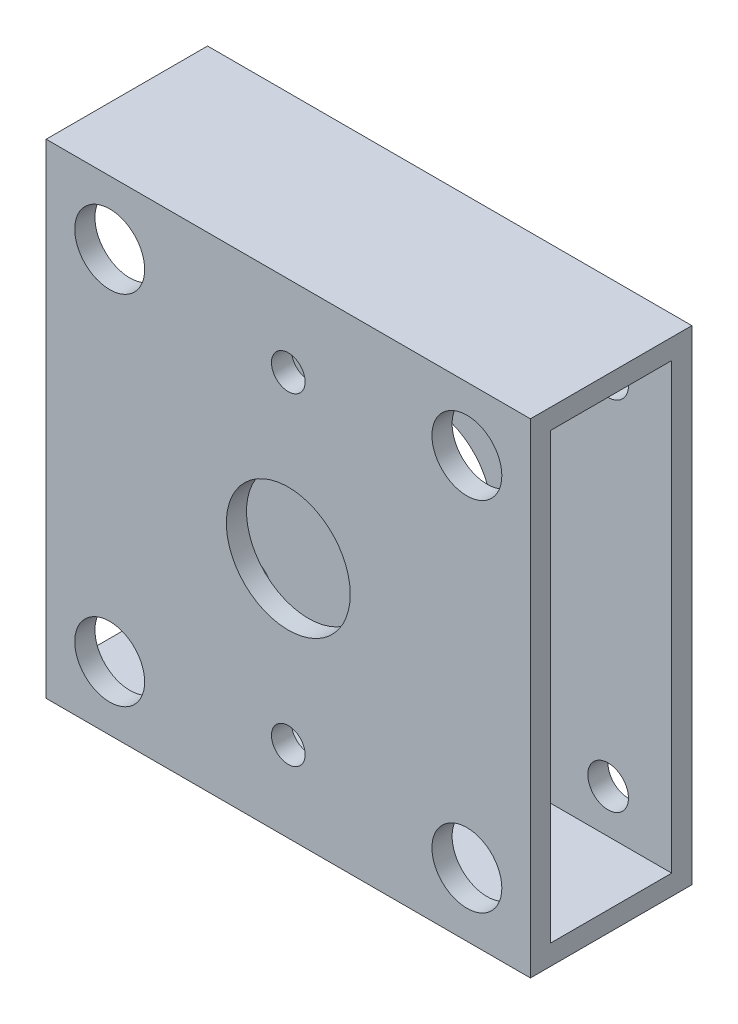
SolidWorks part; units mm, degrees
material "ALUMINUM 6061-T6"
ref_plane "Front Plane" through (0, 0, 0) normal (0, 0, 1) x (1, 0, 0)
ref_plane "Top Plane" through (0, 0, 0) normal (0, 1, 0) x (1, 0, 0)
ref_plane "Right Plane" through (0, 0, 0) normal (1, 0, 0) x (0, 0, -1)
sketch "Sketch1" plane through (0, 0, 0) normal (0, 0, 1) x (1, 0, 0)
  line L1 (-38.1, -38.1) -> (38.1, -38.1)
  line L2 (-38.1, -38.1) -> (-38.1, 38.1)
  line L3 (-38.1, 38.1) -> (38.1, 38.1)
  line L4 (38.1, -38.1) -> (38.1, 38.1)
  line L5 (-38.1, -38.1) -> (38.1, 38.1) construction
  line L6 (-38.1, 38.1) -> (38.1, -38.1) construction
  point P0 (0, 0)
  dimension "D1" = 76.2
  dimension "D2" = 76.2
extrude "Boss-Extrude1" add sketch "Sketch1" along normal mid plane 25.4
sketch "Sketch2" plane through (38.1, 0, 0) normal (1, 0, 0) x (0, 0, -1)
  line L8 (9.525, -34.925) -> (9.525, 34.925)
  line L9 (9.525, 34.925) -> (-9.525, 34.925)
  line L10 (-9.525, 34.925) -> (-9.525, -34.925)
  line L11 (-9.525, -34.925) -> (9.525, -34.925)
  line L12 (9.525, -34.925) -> (9.525, 34.925)
  line L13 (9.525, 34.925) -> (-9.525, 34.925)
  line L14 (-9.525, 34.925) -> (-9.525, -34.925)
  line L15 (-9.525, -34.925) -> (9.525, -34.925)
  dimension "D1" = 3.175
extrude "Cut-Extrude1" cut sketch "Sketch2" against normal through all
sketch "Sketch4" plane through (0, 0, 12.7) normal (0, 0, 1) x (1, 0, 0)
  line L0 (-38.1, 38.1) -> (38.1, -38.1) construction
  line L1 (38.1, -38.1) -> (-38.1, -38.1) construction
  line L2 (-38.1, -38.1) -> (38.1, 38.1) construction
  line L3 (38.1, 38.1) -> (38.1, 0) construction
  line L4 (38.1, -38.1) -> (38.1, 38.1) construction
  line L5 (38.1, 0) -> (-38.1, 0) construction
  line L6 (-38.1, 38.1) -> (-38.1, -38.1) construction
  line L7 (-38.1, 0) -> (-38.1, 38.1) construction
  line L8 (-38.1, 38.1) -> (0, 38.1) construction
  line L9 (38.1, 38.1) -> (-38.1, 38.1) construction
  line L10 (0, 38.1) -> (0, -38.1) construction
  line L11 (0, -38.1) -> (38.1, -38.1) construction
  circle A0 centre (0, 0) radius 9.75
  circle A1 centre (0, 25.4) radius 2.2
  circle A2 centre (-28.1, 28.1) radius 2.369
  circle A3 centre (28.1, 28.1) radius 2.1142
  circle A4 centre (-28.1, -28.1) radius 2.3154
  circle A5 centre (28.1, -28.1) radius 1.7996
  circle A6 centre (0, -25.4) radius 2.2
  dimension "D1" = 19.5
  dimension "D8" = 4.4
  dimension "D9" = 4.4
  dimension "D10" = 4.7379
  dimension "D2" = 25.4
  dimension "D3" = 25.4
  dimension "D5" = 10
extrude "Cut-Extrude2" cut sketch "Sketch4" against normal through all
hole_wizard "CBORE for M6 Socket Head Cap Screw1" positions "Sketch7" profile "Sketch6" counterbore size "M6" standard "Lanco STD" end condition through all
sketch "Sketch7" plane through (0, 0, 12.7) normal (0, 0, 1) x (1, 0, 0)
  point P0 (-28.1, 28.1)
  point P3 (28.1, 28.1)
  point P6 (28.1, -28.1)
  point P9 (-28.1, -28.1)
sketch "Sketch6" plane through (-28.1, 28.1, 12.7) normal (1, 0, 0) x (0, -1, 0)
  line L0 (0, 0) -> (0, 25.4)
  line L1 (0, 25.4) -> (3.2, 25.4)
  line L3 (3.2, 25.4) -> (3.2, 6.4)
  line L4 (3.2, 6.4) -> (5.5, 6.4)
  line L5 (5.5, 6.4) -> (5.5, 0)
  line L7 (5.5, 0) -> (0, 0)
  line L11 (0, -6.35) -> (0, 107.95) construction
  dimension "Thru Hole Dia." = 6.4
  dimension "Thru Hole Depth" = 25.4
  dimension "C'Bore Dia." = 11
  dimension "C'Bore Depth" = 6.4
sketch "Sketch8" plane through (0, 0, -12.7) normal (0, 0, -1) x (-1, 0, 0)
  circle A0 centre (0, 25.4) radius 3.81
  circle A1 centre (0, -25.4) radius 3.81
  dimension "D1" = 7.62
  dimension "D2" = 7.62
extrude "Cut-Extrude3" cut sketch "Sketch8" against normal up to next
sketch "Sketch9" plane through (0, 0, 12.7) normal (0, 0, 1) x (1, 0, 0)
  circle A0 centre (0, 0) radius 31.7771
hole_wizard "CBORE for M5 Socket Head Cap Screw3" positions "Sketch13" profile "Sketch12" counterbore size "M5" standard "Lanco STD" end condition through all
sketch "Sketch13" plane through (0, 0, -12.7) normal (0, 0, -1) x (-1, 0, 0)
  point P0 (0, -25.4)
  point P3 (0, 25.4)
sketch "Sketch12" plane through (0, -25.4, -12.7) normal (1, 0, 0) x (0, 1, 0)
  line L0 (0, 0) -> (0, 25.4)
  line L1 (0, 25.4) -> (2.65, 25.4)
  line L3 (2.65, 25.4) -> (2.65, 5.4)
  line L4 (2.65, 5.4) -> (5, 5.4)
  line L5 (5, 5.4) -> (5, 0)
  line L7 (5, 0) -> (0, 0)
  line L11 (0, -6.35) -> (0, 107.95) construction
  dimension "Thru Hole Dia." = 5.3
  dimension "Thru Hole Depth" = 25.4
  dimension "C'Bore Dia." = 10
  dimension "C'Bore Depth" = 5.4
